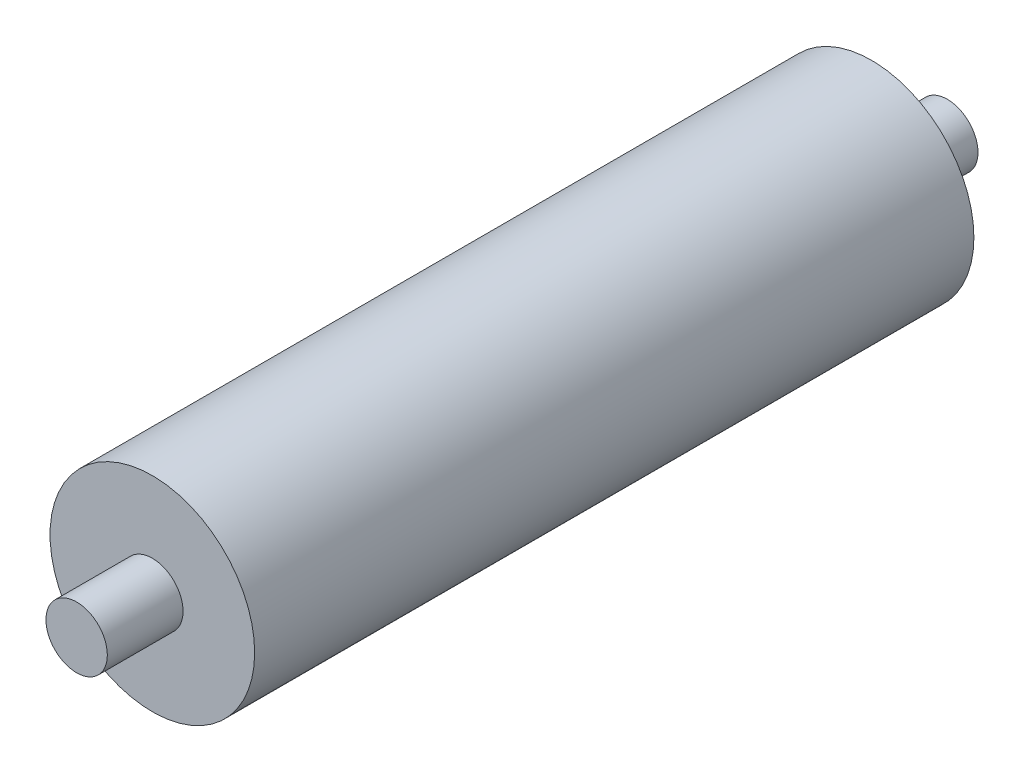
SolidWorks part; units mm, degrees
ref_plane "前视基准面" through (0, 0, 0) normal (0, 0, 1) x (1, 0, 0)
ref_plane "上视基准面" through (0, 0, 0) normal (0, 1, 0) x (1, 0, 0)
ref_plane "右视基准面" through (0, 0, 0) normal (1, 0, 0) x (0, 0, -1)
sketch "草图1" plane through (0, 0, 0) normal (0, 0, 1) x (1, 0, 0)
  circle A0 centre (0, 0) radius 5
  dimension "D1" = 10
extrude "凸台-拉伸1" add sketch "草图1" along normal blind 35.15
sketch "草图2" plane through (0, 0, 0) normal (0, 0, -1) x (-1, 0, 0)
  circle A0 centre (0, 0) radius 1.5
  dimension "D1" = 3
extrude "凸台-拉伸2" add sketch "草图2" along normal blind 3.7
sketch "草图3" plane through (0, 0, 35.15) normal (0, 0, 1) x (1, 0, 0)
  circle A0 centre (0, 0) radius 1.5
  dimension "D1" = 3
extrude "凸台-拉伸3" add sketch "草图3" along normal blind 3.7
